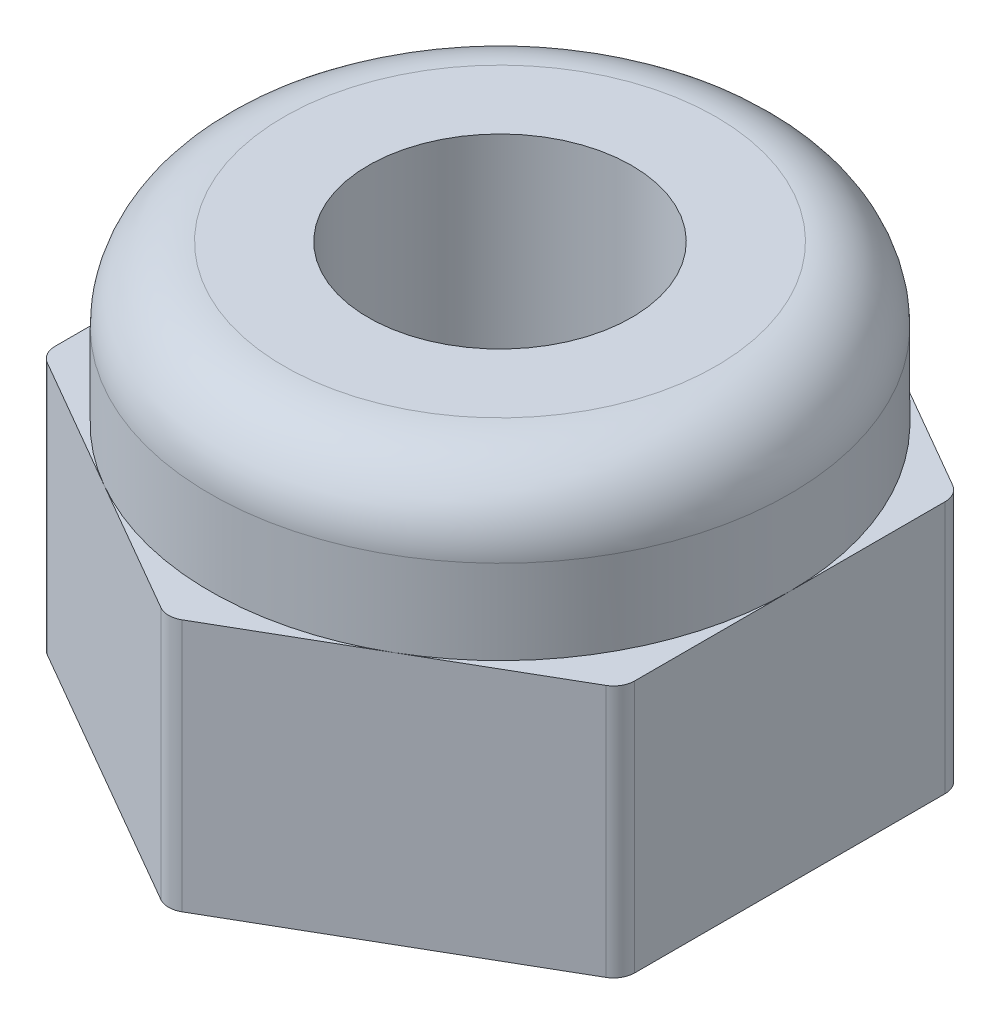
SolidWorks part; units mm, degrees
ref_plane "前视基准面" through (0, 0, 0) normal (0, 0, 1) x (1, 0, 0)
ref_plane "上视基准面" through (0, 0, 0) normal (0, 1, 0) x (1, 0, 0)
ref_plane "右视基准面" through (0, 0, 0) normal (1, 0, 0) x (0, 0, -1)
other "Configuration Table"
sketch "草图1" plane through (0, 0, 0) normal (0, 1, 0) x (1, 0, 0)
  line L1 (2.75, -1.5877) -> (2.75, 1.5877)
  line L2 (2.75, 1.5877) -> (0, 3.1754)
  line L3 (0, 3.1754) -> (-2.75, 1.5877)
  line L4 (-2.75, 1.5877) -> (-2.75, -1.5877)
  line L5 (-2.75, -1.5877) -> (0, -3.1754)
  line L6 (0, -3.1754) -> (2.75, -1.5877)
  circle A0 centre (0, 0) radius 2.75 construction
  dimension "D1" = 5.5
extrude "凸台-拉伸1" add sketch "草图1" along normal blind 2.4
sketch "草图2" plane through (0, 0, 0) normal (0, -1, 0) x (1, 0, 0)
  line L0 (2.75, 1.5877) -> (2.75, -1.5877) construction
  circle A0 centre (0, 0) radius 2.75
extrude "凸台-拉伸2" add sketch "草图2" against normal blind 3.9
fillet "圆角1" radius 0.7 1 edges at (0, 3.9, -2.75)
fillet "圆角2" radius 0.2 6 edges at (2.75, 1.2, -1.5877) (2.75, 1.2, 1.5877) (0, 1.2, 3.1754) (-2.75, 1.2, 1.5877) (-2.75, 1.2, -1.5877) (0, 1.2, -3.1754)
hole_wizard "M3 螺纹孔1" positions "草图3" profile "草图5" tap size "M3" standard "GB"
sketch "草图3" plane through (0, 0, 0) normal (0, -1, 0) x (-1, 0, 0)
  point P0 (0, 0)
sketch "草图5" plane through (0, 0, 0) normal (1, 0, 0) x (0, 0, -1)
  line L0 (0, 0) -> (0, 8.2511)
  line L1 (0, 8.2511) -> (1.25, 7.5)
  line L2 (1.25, 7.5) -> (1.25, 0.275)
  line L3 (1.25, 0.275) -> (1.525, 0)
  line L5 (1.525, 0) -> (0, 0)
  line L6 (-1.25, 0.275) -> (-1.525, 0) construction
  line L10 (0, 8.2511) -> (-1.25, 7.5) construction
  line L11 (0, -6.35) -> (0, 107.95) construction
  dimension "螺纹孔钻头直径" = 2.5
  dimension "螺纹孔钻头深度" = 7.5
  dimension "近端锥形沉头孔直径" = 3.05
  dimension "近端锥形沉头孔角度" = 90
  dimension "导头角度" = 118
cosmetic thread "孔螺蚊线1" parameters "D1"=6, "D2"=3
